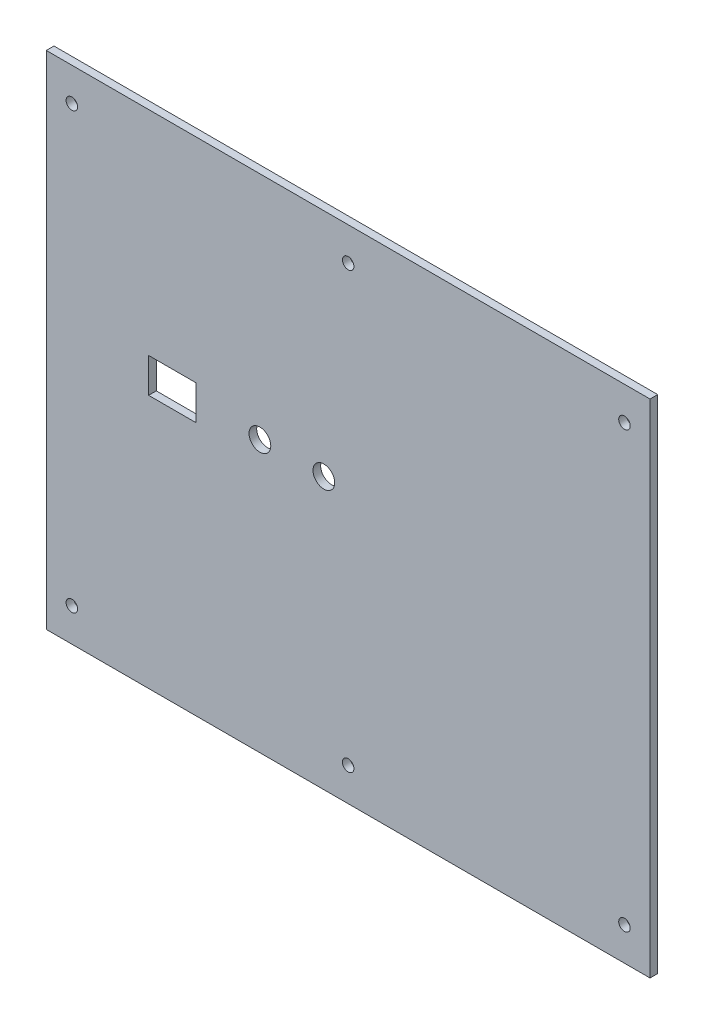
SolidWorks part; units mm, degrees
ref_plane "Спереди" through (0, 0, 0) normal (0, 0, 1) x (1, 0, 0)
ref_plane "Сверху" through (0, 0, 0) normal (0, 1, 0) x (1, 0, 0)
ref_plane "Справа" through (0, 0, 0) normal (1, 0, 0) x (0, 0, -1)
sketch "Эскиз1" plane through (0, 0, 0) normal (0, 0, 1) x (1, 0, 0)
  line L0 (0, 0) -> (236, 0)
  line L1 (0, 0) -> (0, 196)
  line L2 (236, 0) -> (236, 196)
  line L3 (0, 196) -> (236, 196)
  line L4 (10, 183) -> (226, 183) construction
  line L5 (10, 183) -> (10, 13) construction
  line L6 (226, 183) -> (226, 13) construction
  line L7 (10, 13) -> (226, 13) construction
  circle A0 centre (10, 183) radius 2.25
  circle A1 centre (10, 13) radius 2.25
  circle A2 centre (226, 183) radius 2.25
  circle A3 centre (226, 13) radius 2.25
  circle A4 centre (118, 183) radius 2.25
  circle A5 centre (118, 13) radius 2.25
  dimension "D7" = 4.5
  dimension "D8" = 4.5
  dimension "D9" = 4.5
  dimension "D10" = 4.5
  dimension "D11" = 4.5
  dimension "D12" = 4.5
  dimension "D1" = 236
  dimension "D2" = 196
  dimension "D3" = 10
  dimension "D4" = 13
  dimension "D5" = 10
  dimension "D6" = 13
extrude "Бобышка-Вытянуть1" add sketch "Эскиз1" along normal blind 3
sketch "Эскиз2" plane through (0, 0, 3) normal (0, 0, 1) x (1, 0, 0)
  line L7 (236, 196) -> (0, 196) construction
  line L8 (0, 106) -> (108.5, 106) construction
  line L9 (0, 196) -> (0, 0) construction
  line L10 (40, 112.75) -> (58.5, 112.75)
  line L11 (40, 112.75) -> (40, 99.25)
  line L12 (58.5, 112.75) -> (58.5, 99.25)
  line L13 (40, 99.25) -> (58.5, 99.25)
  line L14 (40, 106) -> (58.5, 106) construction
  circle A2 centre (108.5, 106) radius 4.25
  circle A3 centre (83.5, 106) radius 4.25
  dimension "D9" = 13.5
  dimension "D13" = 25
  dimension "D14" = 25
  dimension "D15" = 8.5
  dimension "D16" = 8.5
  dimension "D10" = 18.5
  dimension "D11" = 40
  dimension "D12" = 90
extrude "Вырез-Вытянуть1" cut sketch "Эскиз2" against normal through all
